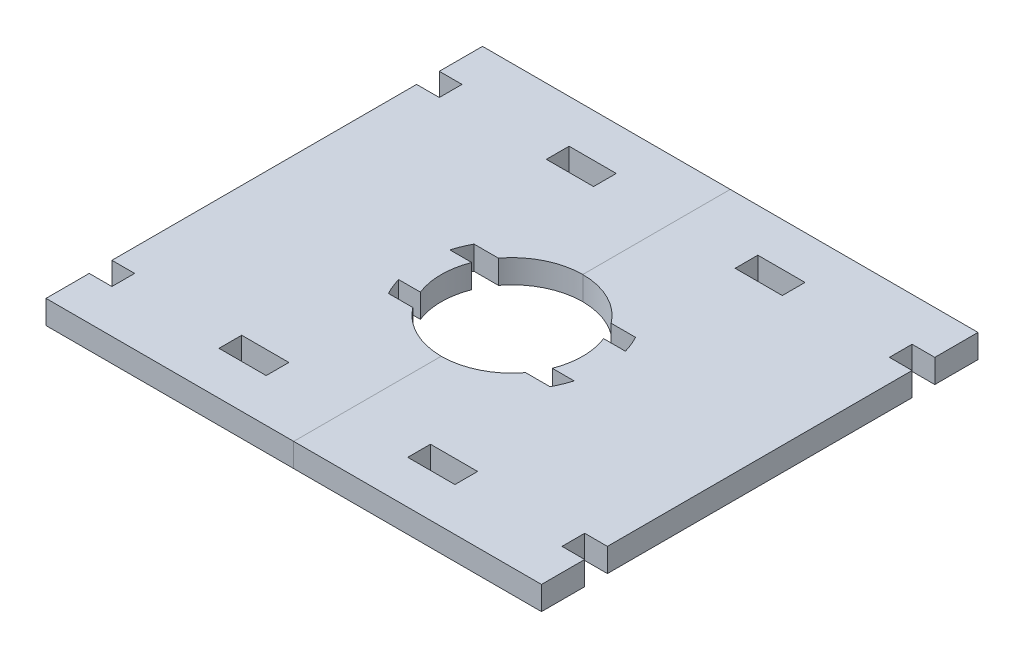
SolidWorks part; units mm, degrees
ref_plane "Front Plane" through (0, 0, 0) normal (0, 0, 1) x (1, 0, 0)
ref_plane "Top Plane" through (0, 0, 0) normal (0, 1, 0) x (1, 0, 0)
ref_plane "Right Plane" through (0, 0, 0) normal (1, 0, 0) x (0, 0, -1)
sketch "Sketch1" plane through (0, 0, 0) normal (0, 1, 0) x (1, 0, 0)
  line L0 (-15.5, 7.25) -> (-13.6999, 7.25) construction
  line L1 (-13.6999, -7.25) -> (-9.5623, -7.25)
  line L2 (-15.5, -7.25) -> (-15.5, -4.35) construction
  line L3 (-13.6999, 7.25) -> (-9.5623, 7.25)
  line L4 (15.5, 4.35) -> (15.5, 7.25) construction
  line L5 (-14.04, -6.5671) -> (-10.8697, -5.0842) construction
  line L6 (-14.04, 6.5671) -> (-10.8697, 5.0842) construction
  line L7 (-14.8771, -4.35) -> (-11.1838, -4.35)
  line L8 (-15.5, -4.35) -> (-15.5, 0) construction
  line L9 (-14.8771, 4.35) -> (-11.1838, 4.35)
  line L10 (15.5, 0) -> (15.5, 4.35) construction
  line L11 (-14.9234, -4.1882) -> (14.9234, 4.1882) construction
  line L12 (-14.9234, 4.1882) -> (14.9234, -4.1882) construction
  line L13 (-15.5, 7.25) -> (-14.04, 6.5671) construction
  line L14 (-15.5, 4.35) -> (-15.5, 7.25) construction
  line L15 (-15.5, 4.35) -> (-14.8771, 4.35) construction
  line L16 (-15.5, 4.35) -> (-14.9234, 4.1882) construction
  line L17 (-15.5, 0) -> (-15.5, 4.35) construction
  line L18 (-15.5, 0) -> (-15.5, 4.35) construction
  line L19 (-15.5, -4.35) -> (-15.5, 0) construction
  line L20 (-15.5, -4.35) -> (-14.9234, -4.1882) construction
  line L21 (-15.5, -4.35) -> (-14.8771, -4.35) construction
  line L22 (-15.5, -7.25) -> (-14.04, -6.5671) construction
  line L23 (-15.5, -7.25) -> (-13.6999, -7.25) construction
  line L24 (15.5, -7.25) -> (15.5, -4.35) construction
  line L25 (14.04, -6.5671) -> (15.5, -7.25) construction
  line L26 (13.6999, -7.25) -> (15.5, -7.25) construction
  line L27 (15.5, -4.35) -> (15.5, 0) construction
  line L28 (15.5, -4.35) -> (15.5, 0) construction
  line L29 (15.5, 0) -> (15.5, 4.35) construction
  line L30 (14.9234, 4.1882) -> (15.5, 4.35) construction
  line L31 (14.8771, 4.35) -> (15.5, 4.35) construction
  line L32 (13.6999, 7.25) -> (15.5, 7.25) construction
  line L33 (14.9234, -4.1882) -> (15.5, -4.35) construction
  line L34 (14.8771, -4.35) -> (15.5, -4.35) construction
  line L35 (-9.5623, 7.25) -> (9.5623, 7.25) construction
  line L36 (9.5623, 7.25) -> (13.6999, 7.25)
  line L37 (-9.3, 4.35) -> (9.3, 4.35) construction
  line L38 (11.1838, 4.35) -> (14.8771, 4.35)
  line L39 (-10.8697, 5.0842) -> (-9.3, 4.35) construction
  line L40 (-9.3, 4.35) -> (9.3, -4.35) construction
  line L41 (-11.1838, 4.35) -> (-9.3, 4.35) construction
  line L42 (-9.5623, -7.25) -> (9.5623, -7.25) construction
  line L43 (9.5623, -7.25) -> (13.6999, -7.25)
  line L44 (-9.3, -4.35) -> (9.3, -4.35) construction
  line L45 (11.1838, -4.35) -> (14.8771, -4.35)
  line L46 (-10.8697, -5.0842) -> (-9.3, -4.35) construction
  line L47 (-9.3, -4.35) -> (9.3, 4.35) construction
  line L48 (-11.1838, -4.35) -> (-9.3, -4.35) construction
  line L49 (9.3, -4.35) -> (11.1838, -4.35) construction
  line L50 (9.3, -4.35) -> (10.8697, -5.0842) construction
  line L51 (10.8697, -5.0842) -> (14.04, -6.5671) construction
  line L52 (9.3, 4.35) -> (11.1838, 4.35) construction
  line L53 (9.3, 4.35) -> (10.8697, 5.0842) construction
  line L54 (10.8697, 5.0842) -> (15.5, 7.25) construction
  arc A0 (-11.1838, 4.35) -> (-11.1838, -4.35) centre (0, 0) ccw
  arc A1 (-13.6999, 7.25) -> (-14.9234, 4.1882) centre (0, 0) ccw
  arc A2 (13.6999, 7.25) -> (-13.6999, 7.25) centre (0, 0) ccw construction
  arc A3 (-13.6999, -7.25) -> (13.6999, -7.25) centre (0, 0) ccw construction
  arc A4 (13.6999, -7.25) -> (14.9234, -4.1882) centre (0, 0) ccw
  arc A5 (15.5, 0) -> (14.9234, 4.1882) centre (0, 0) ccw construction
  arc A6 (14.9234, 4.1882) -> (13.6999, 7.25) centre (0, 0) ccw
  arc A7 (14.9234, -4.1882) -> (15.5, 0) centre (0, 0) ccw construction
  arc A8 (-14.9234, 4.1882) -> (-15.5, 0) centre (0, 0) ccw construction
  arc A9 (-14.9234, -4.1882) -> (-13.6999, -7.25) centre (0, 0) ccw
  arc A10 (-15.5, 0) -> (-14.9234, -4.1882) centre (0, 0) ccw construction
  arc A11 (-9.5623, 7.25) -> (-10.8697, 5.0842) centre (0, 0) ccw construction
  arc A12 (-10.8697, 5.0842) -> (-11.1838, 4.35) centre (0, 0) ccw construction
  arc A13 (-10.8697, -5.0842) -> (-9.5623, -7.25) centre (0, 0) ccw construction
  arc A14 (-9.5623, -7.25) -> (9.5623, -7.25) centre (0, 0) ccw
  arc A15 (-11.1838, -4.35) -> (-10.8697, -5.0842) centre (0, 0) ccw construction
  arc A16 (10.8697, -5.0842) -> (11.1838, -4.35) centre (0, 0) ccw construction
  arc A17 (11.1838, -4.35) -> (-9.5623, 7.25) centre (0, 0) ccw
  arc A18 (9.5623, -7.25) -> (10.8697, -5.0842) centre (0, 0) ccw construction
  dimension "D1" = 24
  dimension "D2" = 31
  dimension "D3" = 14.5
  dimension "D4" = 8.7
sketch "Sketch2" plane through (0, 0, 0) normal (0, 1, 0) x (1, 0, 0)
  line L0 (11.1838, -4.35) -> (14.8771, -4.35) construction
  line L1 (-13.6999, 7.25) -> (-9.5623, 7.25) construction
  line L2 (-14.8771, -4.35) -> (-11.1838, -4.35) construction
  line L3 (-14.8771, 4.35) -> (-11.1838, 4.35) construction
  line L4 (9.5623, -7.25) -> (13.6999, -7.25) construction
  line L5 (-13.6999, -7.25) -> (-9.5623, -7.25) construction
  line L6 (9.5623, 7.25) -> (13.6999, 7.25) construction
  line L7 (11.1838, 4.35) -> (14.8771, 4.35) construction
  line L8 (11.1838, -4.35) -> (14.8771, -4.35)
  line L9 (-13.6999, 7.25) -> (-9.5623, 7.25)
  line L10 (-14.8771, -4.35) -> (-11.1838, -4.35)
  line L11 (-14.8771, 4.35) -> (-11.1838, 4.35)
  line L12 (9.5623, -7.25) -> (13.6999, -7.25)
  line L13 (-13.6999, -7.25) -> (-9.5623, -7.25)
  line L14 (9.5623, 7.25) -> (13.6999, 7.25)
  line L15 (11.1838, 4.35) -> (14.8771, 4.35)
  line L17 (-42, -37) -> (42, -37)
  line L18 (-42, -37) -> (-42, 37)
  line L19 (-42, 37) -> (42, 37)
  line L20 (42, -37) -> (42, 37)
  line L21 (-42, -37) -> (42, 37) construction
  line L22 (-42, 37) -> (42, -37) construction
  arc A0 (11.1838, -4.35) -> (-9.5623, 7.25) centre (0, 0) ccw construction
  arc A1 (-13.6999, 7.25) -> (-14.9234, 4.1882) centre (0, 0) ccw construction
  arc A2 (-11.1838, 4.35) -> (-11.1838, -4.35) centre (0, 0) ccw construction
  arc A3 (13.6999, -7.25) -> (14.9234, -4.1882) centre (0, 0) ccw construction
  arc A4 (-9.5623, -7.25) -> (9.5623, -7.25) centre (0, 0) ccw construction
  arc A5 (-14.9234, -4.1882) -> (-13.6999, -7.25) centre (0, 0) ccw construction
  arc A6 (14.9234, 4.1882) -> (13.6999, 7.25) centre (0, 0) ccw construction
  arc A7 (11.1838, -4.35) -> (-9.5623, 7.25) centre (0, 0) ccw
  arc A8 (-13.6999, 7.25) -> (-14.9234, 4.1882) centre (0, 0) ccw
  arc A9 (-11.1838, 4.35) -> (-11.1838, -4.35) centre (0, 0) ccw
  arc A10 (13.6999, -7.25) -> (14.9234, -4.1882) centre (0, 0) ccw
  arc A11 (-9.5623, -7.25) -> (9.5623, -7.25) centre (0, 0) ccw
  arc A12 (-14.9234, -4.1882) -> (-13.6999, -7.25) centre (0, 0) ccw
  arc A13 (14.9234, 4.1882) -> (13.6999, 7.25) centre (0, 0) ccw
  dimension "D1" = 84
  dimension "D2" = 74
extrude "Boss-Extrude1" add sketch "Sketch2" along normal blind 4
split "Split1" trim tools "Right Plane" bodies to split 101 resulting bodies 102 103
sketch "Sketch4" plane through (0, 4, 0) normal (0, 1, 0) x (1, 0, 0)
  line L0 (0, -18.5) -> (42, -18.5) construction
  line L2 (42, -37) -> (42, 37) construction
  line L3 (0, -18.5) -> (0, -37) construction
  line L4 (-42, -37) -> (-42, 37) construction
  line L5 (-20, -29.675) -> (-12, -29.675)
  line L6 (-20, -29.675) -> (-20, -25.825)
  line L7 (-20, -25.825) -> (-12, -25.825)
  line L8 (-12, -29.675) -> (-12, -25.825)
  line L9 (-20, -29.675) -> (-12, -25.825) construction
  line L10 (-20, -25.825) -> (-12, -29.675) construction
  line L11 (-42, -29.675) -> (-38.15, -29.675)
  line L12 (-42, -29.675) -> (-42, -25.825)
  line L13 (-42, -25.825) -> (-38.15, -25.825)
  line L14 (-38.15, -29.675) -> (-38.15, -25.825)
  line L15 (-42, -29.675) -> (-38.15, -25.825) construction
  line L16 (-42, -25.825) -> (-38.15, -29.675) construction
  line L17 (0, 0) -> (0, -37) construction
  line L33 (42, -25.825) -> (38.15, -29.675) construction
  line L34 (42, -29.675) -> (38.15, -25.825) construction
  line L35 (20, -25.825) -> (12, -29.675) construction
  line L36 (20, -29.675) -> (12, -25.825) construction
  line L45 (38.15, -29.675) -> (38.15, -25.825)
  line L46 (42, -25.825) -> (38.15, -25.825)
  line L47 (42, -29.675) -> (42, -25.825)
  line L48 (42, -29.675) -> (38.15, -29.675)
  line L49 (12, -29.675) -> (12, -25.825)
  line L50 (20, -25.825) -> (12, -25.825)
  line L51 (20, -29.675) -> (20, -25.825)
  line L52 (20, -29.675) -> (12, -29.675)
  line L53 (-2.2, 0) -> (2.2, 0) construction
  line L54 (20, 29.675) -> (12, 25.825) construction
  line L55 (20, 25.825) -> (12, 29.675) construction
  line L56 (42, 29.675) -> (38.15, 25.825) construction
  line L57 (42, 25.825) -> (38.15, 29.675) construction
  line L58 (20, 29.675) -> (12, 29.675)
  line L59 (20, 29.675) -> (20, 25.825)
  line L60 (20, 25.825) -> (12, 25.825)
  line L61 (12, 29.675) -> (12, 25.825)
  line L62 (42, 29.675) -> (38.15, 29.675)
  line L63 (42, 29.675) -> (42, 25.825)
  line L64 (42, 25.825) -> (38.15, 25.825)
  line L65 (38.15, 29.675) -> (38.15, 25.825)
  line L82 (-42, 25.825) -> (-38.15, 29.675) construction
  line L83 (-42, 29.675) -> (-38.15, 25.825) construction
  line L84 (-20, 25.825) -> (-12, 29.675) construction
  line L85 (-20, 29.675) -> (-12, 25.825) construction
  line L94 (-38.15, 29.675) -> (-38.15, 25.825)
  line L95 (-42, 25.825) -> (-38.15, 25.825)
  line L96 (-42, 29.675) -> (-42, 25.825)
  line L97 (-42, 29.675) -> (-38.15, 29.675)
  line L98 (-12, 29.675) -> (-12, 25.825)
  line L99 (-20, 25.825) -> (-12, 25.825)
  line L100 (-20, 29.675) -> (-20, 25.825)
  line L101 (-20, 29.675) -> (-12, 29.675)
  point P6 (-16, -27.75)
  point P14 (0, -27.75)
  point P15 (-40.075, -27.75)
  point P53 (40.075, -27.75)
  point P54 (16, -27.75)
  point P65 (16, 27.75)
  point P66 (40.075, 27.75)
  point P95 (-40.075, 27.75)
  point P96 (-16, 27.75)
  dimension "D1" = 3.85
  dimension "D2" = 8
  dimension "D3" = 20
  dimension "D4" = 3.85
extrude "Cut-Extrude2" cut sketch "Sketch4" against normal through all both
equation "\"m3_hole\"= 3.5"
equation "\"m3_washer\"= 7.3"
equation "\"m3_nut\"= 5.3"
equation "\"guide_width\"= 10.0"
equation "\"guide_length\"= 65.0"
equation "\"guide_tab_length\" = 10.0"
equation "\"guide_tab_width\" = 9.0"
equation "\"guide_thickness\" = 12.0"
equation "\"grinder_od\"= 52.0"
equation "\"grinder_id\"= 45.5"
equation "\"grinder_adjust_od\" = 58.0"
equation "\"funnel_width_from_adjust_ring\" = 13.0"
equation "\"drill_contact_diameter_small\" = 24.0"
equation "\"drill_contact_diameter_medium\" = 28.0"
equation "\"drill_contact_diameter_large\" = 39.0"
equation "\"drill_contact_diameter_tab\" = 31.0"
equation "\"drill_contact_ow_tab\" = 14.5"
equation "\"drill_contact_iw_tab\" = 8.7"
equation "\"drill_contact_small_height\" = 15.5"
equation "\"drill_contact_large_height\" = 34.5"
equation "\"D1@Sketch1\"=\"drill_contact_diameter_small\""
equation "\"D2@Sketch1\"=\"drill_contact_diameter_tab\""
equation "\"D3@Sketch1\"=\"drill_contact_ow_tab\""
equation "\"D1@Sketch2\"=\"grinder_od\"+\"guide_thickness\"+20"
equation "\"D2@Sketch2\"=\"grinder_od\"+\"guide_thickness\"+\"guide_tab_length\""
equation "\"plywood_thickness\" = 3.85"
equation "\"D4@Sketch1\"=\"drill_contact_iw_tab\""
equation "\"plywood_peg_length\" = 40.0"
equation "\"plywood_peg_width\" = 8.0"
equation "\"D3@Sketch4\"=\"plywood_peg_length\"/2"
equation "\"D2@Sketch4\"=\"plywood_peg_width\""
equation "\"D1@Sketch4\"=\"plywood_thickness\""
equation "\"D4@Sketch4\"=\"plywood_thickness\""
